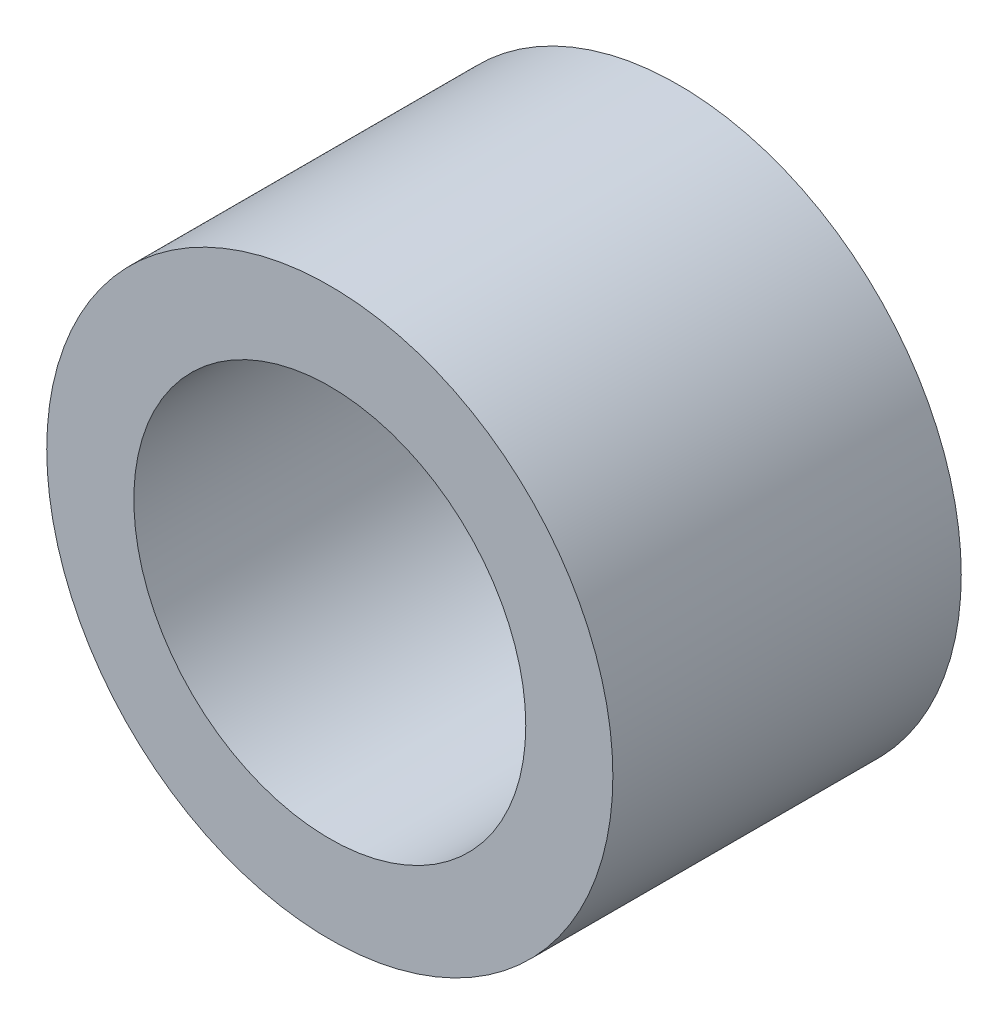
SolidWorks part; units mm, degrees
ref_plane "Front Plane" through (0, 0, 0) normal (0, 0, 1) x (1, 0, 0)
ref_plane "Top Plane" through (0, 0, 0) normal (0, 1, 0) x (1, 0, 0)
ref_plane "Right Plane" through (0, 0, 0) normal (1, 0, 0) x (0, 0, -1)
sketch "Sketch1" plane through (0, 0, 0) normal (0, 0, 1) x (1, 0, 0)
  circle A0 centre (0, 0) radius 2.25
  circle A1 centre (0, 0) radius 3.25
  dimension "D1" = 4.5
  dimension "D2" = 6.5
extrude "Boss-Extrude1" add sketch "Sketch1" along normal blind 4
